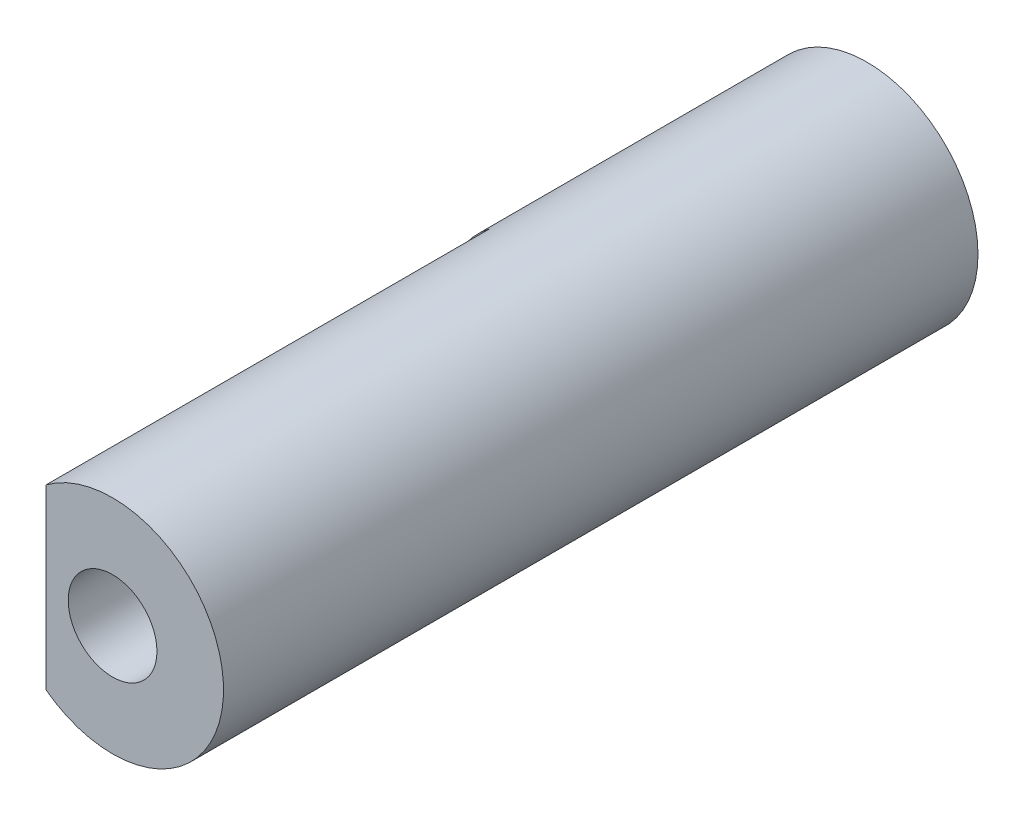
SolidWorks part; units mm, degrees
material "AISI 1020"
ref_plane "Front Plane" through (0, 0, 0) normal (0, 0, 1) x (1, 0, 0)
ref_plane "Top Plane" through (0, 0, 0) normal (0, 1, 0) x (1, 0, 0)
ref_plane "Right Plane" through (0, 0, 0) normal (1, 0, 0) x (0, 0, -1)
sketch "Sketch1" plane through (0, 0, 0) normal (0, 0, 1) x (1, 0, 0)
  circle A0 centre (0, 0) radius 2.5
  dimension "D1" = 5
extrude "Boss-Extrude1" add sketch "Sketch1" along normal blind 17
sketch "Sketch2" plane through (0, 0, 17) normal (0, 0, 1) x (1, 0, 0)
  line L1 (-2.5, 2.5) -> (-1.5, 2.5)
  line L2 (-2.5, 2.5) -> (-2.5, -2.5)
  line L3 (-2.5, -2.5) -> (-1.5, -2.5)
  line L4 (-1.5, 2.5) -> (-1.5, -2.5)
  dimension "D1" = 1
  dimension "D2" = 1.5
  dimension "D3" = 5
  dimension "D4" = 2.5
extrude "Cut-Extrude1" cut sketch "Sketch2" against normal blind 10
sketch "Sketch3" plane through (0, 0, 17) normal (0, 0, 1) x (1, 0, 0)
  circle A0 centre (0, 0) radius 1
  dimension "D1" = 2
extrude "Cut-Extrude2" cut sketch "Sketch3" against normal blind 2
